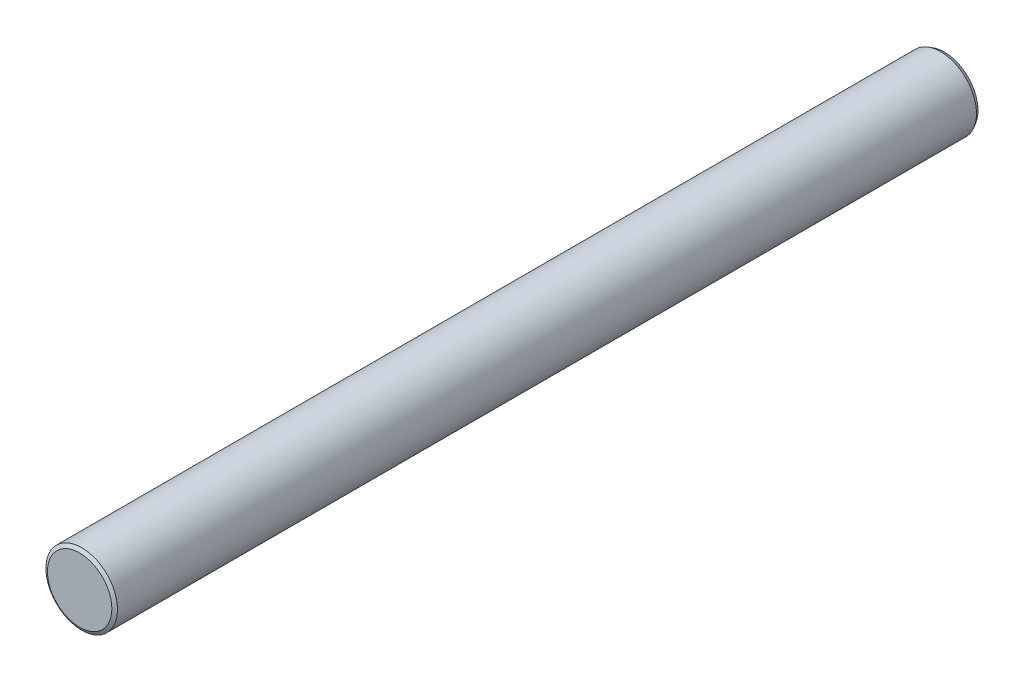
SolidWorks part; units mm, degrees
ref_plane "Front Plane" through (0, 0, 0) normal (0, 0, 1) x (1, 0, 0)
ref_plane "Top Plane" through (0, 0, 0) normal (0, 1, 0) x (1, 0, 0)
ref_plane "Right Plane" through (0, 0, 0) normal (1, 0, 0) x (0, 0, -1)
sketch "Sketch1" plane through (0, 0, 0) normal (0, 0, 1) x (1, 0, 0)
  circle A0 centre (0, 0) radius 3.475
  dimension "D1" = 6.95
extrude "Boss-Extrude1" add sketch "Sketch1" along normal mid plane 84
chamfer "Chamfer1" distance 0.2 angle 60 2 edges at (3.475, 0, -42) (3.475, 0, 42)
